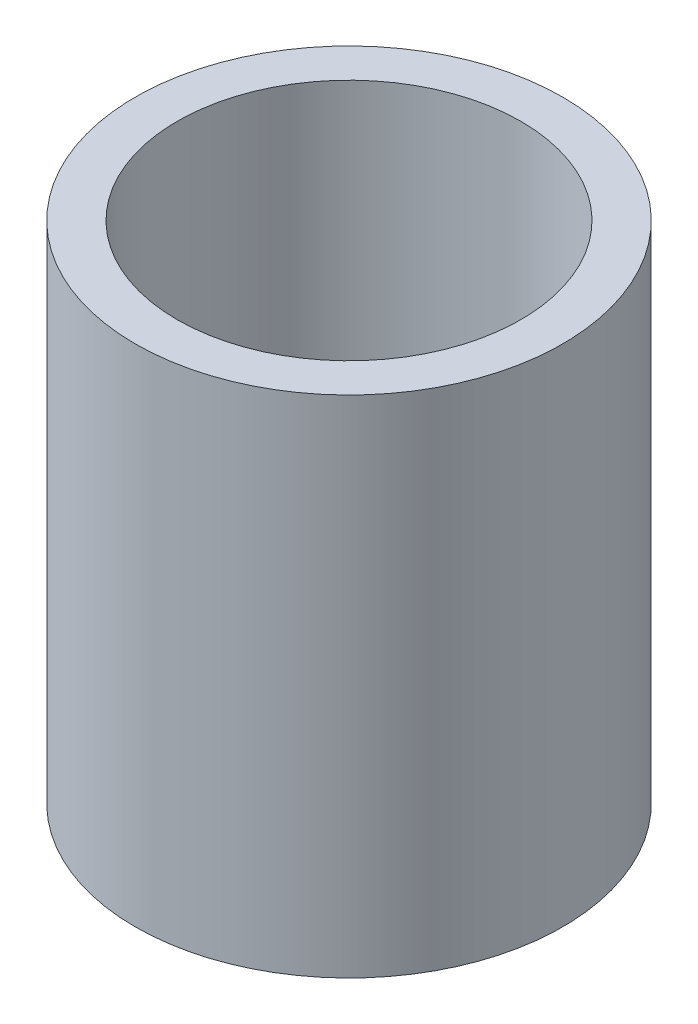
SolidWorks part; units mm, degrees
ref_plane "Front Plane" through (0, 0, 0) normal (0, 0, 1) x (1, 0, 0)
ref_plane "Top Plane" through (0, 0, 0) normal (0, 1, 0) x (1, 0, 0)
ref_plane "Right Plane" through (0, 0, 0) normal (1, 0, 0) x (0, 0, -1)
sketch "Sketch1" plane through (0, 70.2663, 0) normal (0, -1, 0) x (1, 0, 0)
  circle A0 centre (0, 0) radius 5.1054
  circle A1 centre (0, 0) radius 6.35
  dimension "D1" = 12.7
  dimension "D2" = 10.2108
extrude "Boss-Extrude1" add sketch "Sketch1" along normal blind 15
